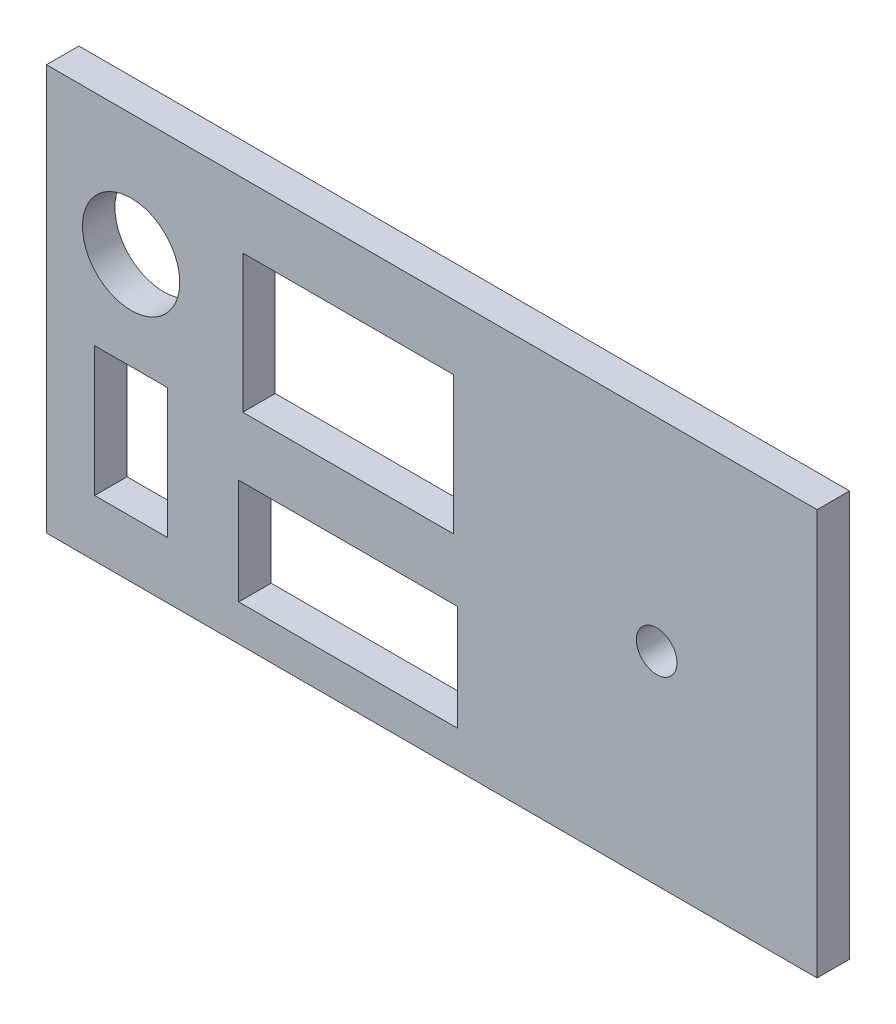
SolidWorks part; units mm, degrees
ref_plane "Front Plane" through (0, 0, 0) normal (0, 0, 1) x (1, 0, 0)
ref_plane "Top Plane" through (0, 0, 0) normal (0, 1, 0) x (1, 0, 0)
ref_plane "Right Plane" through (0, 0, 0) normal (1, 0, 0) x (0, 0, -1)
sketch "Sketch3" plane through (0, 0, 0) normal (0, 0, 1) x (1, 0, 0)
  line L0 (-87.0985, -48.7036) -> (-61.0985, -48.7036)
  line L1 (-61.0985, -48.7036) -> (-61.0985, -31.7036)
  line L2 (-61.0985, -31.7036) -> (-87.0985, -31.7036)
  line L3 (-87.0985, -31.7036) -> (-87.0985, -48.7036)
  line L4 (-87.5985, -69.2036) -> (-60.5985, -69.2036)
  line L5 (-60.5985, -69.2036) -> (-60.5985, -56.2036)
  line L6 (-60.5985, -56.2036) -> (-87.5985, -56.2036)
  line L7 (-87.5985, -56.2036) -> (-87.5985, -69.2036)
  line L8 (-111.2985, -73.7036) -> (-16.2985, -73.7036)
  line L9 (-16.2985, -73.7036) -> (-16.2985, -23.7036)
  line L10 (-16.2985, -23.7036) -> (-111.2985, -23.7036)
  line L11 (-111.2985, -23.7036) -> (-111.2985, -73.7036)
  line L12 (-105.3596, -66.7221) -> (-96.3596, -66.7221)
  line L13 (-96.3596, -66.7221) -> (-96.3596, -50.7221)
  line L14 (-96.3596, -50.7221) -> (-105.3596, -50.7221)
  line L15 (-105.3596, -50.7221) -> (-105.3596, -66.7221)
  ellipse E0 centre (-36.0722, -48.7036) end of major axis (-36.0722, -46.2036) minor radius 2.5
  ellipse E1 centre (-100.8596, -38.7221) end of major axis (-106.8596, -38.7221) minor radius 6
extrude "Boss-Extrude2" add sketch "Sketch3" along normal blind 4
